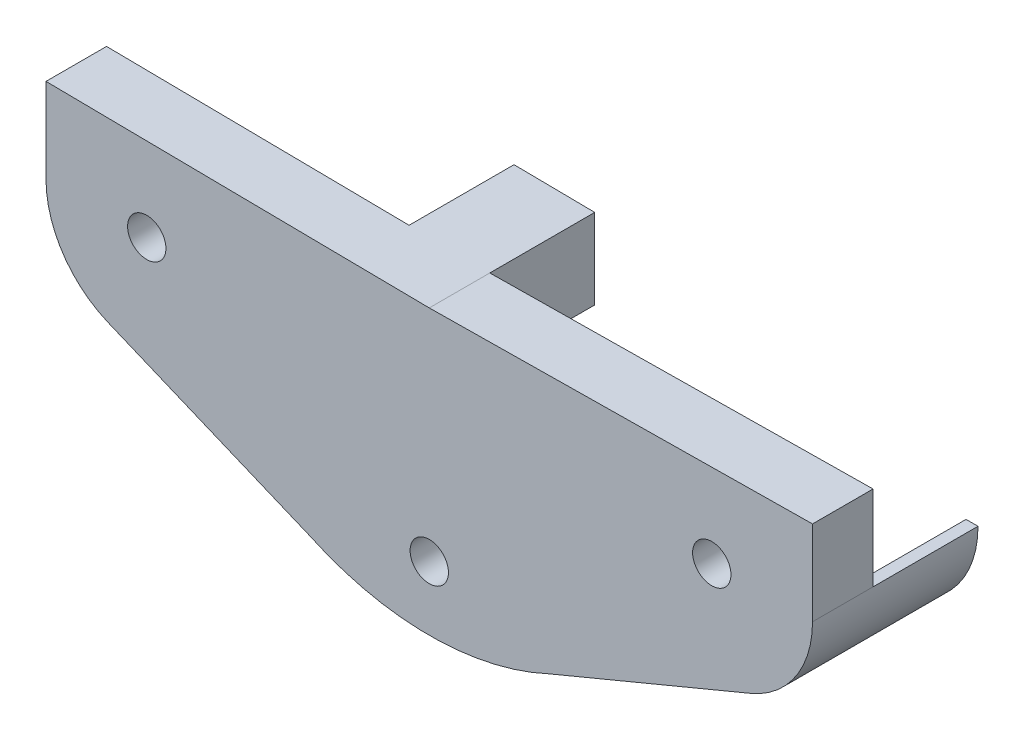
SolidWorks part; units mm, degrees
ref_plane "前视基准面" through (0, 0, 0) normal (0, 0, 1) x (1, 0, 0)
ref_plane "上视基准面" through (0, 0, 0) normal (0, 1, 0) x (1, 0, 0)
ref_plane "右视基准面" through (0, 0, 0) normal (1, 0, 0) x (0, 0, -1)
sketch "草图1" plane through (0, 0, 0) normal (0, 0, 1) x (1, 0, 0)
  line L0 (0, 14.4266) -> (0, -15.1664) construction
  line L1 (5.9425, -8.6841) -> (15.918, -4.5332)
  line L2 (-18.9924, 0.0761) -> (-18.9924, 4.276)
  line L3 (-18.9924, 4.276) -> (0, 4.0495)
  line L4 (18.9924, 4.276) -> (0, 4.0495)
  line L5 (18.9924, 0.0761) -> (18.9924, 4.276)
  line L6 (-5.9425, -8.6841) -> (-15.918, -4.5332)
  circle A0 centre (-14, 0.0761) radius 0.95
  arc A2 (15.918, -4.5332) -> (18.9924, 0.0761) centre (14, 0.0761) ccw
  circle A3 centre (14, 0.0761) radius 0.95
  arc A4 (-15.918, -4.5332) -> (-18.9924, 0.0761) centre (-14, 0.0761) cw
  arc A5 (-5.9425, -8.6841) -> (5.9425, -8.6841) centre (0, 4.0495) ccw
  circle A7 centre (0, -6.8345) radius 0.95
  point P20 (0, 4.0495)
extrude "凸台-拉伸1" add sketch "草图1" along normal blind 3
sketch "草图2" plane through (0, 0, 0) normal (0, 0, -1) x (-1, 0, 0)
  line L0 (-15.918, -4.5332) -> (-15.6904, -3.9862)
  line L1 (0, 4.0495) -> (3.9997, 4.0972)
  line L3 (-18.4, 0.0761) -> (-19, 0.0761)
  line L4 (0, 4.0495) -> (0, 0.0761)
  line L5 (0, 4.0495) -> (18.9924, 4.276) construction
  line L6 (3.9997, 4.0972) -> (3.9997, 0)
  line L8 (3.9997, 0) -> (0, 0.0761)
  arc A0 (-18.4, 0.0761) -> (-15.6904, -3.9862) centre (-14, 0.0761) ccw
  arc A3 (-18.9924, 0.0761) -> (-15.918, -4.5332) centre (-14, 0.0761) ccw construction
  arc A4 (-18.9924, 0.0761) -> (-15.918, -4.5332) centre (-14, 0.0761) ccw
  arc M28 (-18.9924, 0.0761) -> (-15.918, -4.5332) centre (-14, 0.0761) ccw
  line M34 (18.9924, 4.276) -> (0, 4.0495)
extrude "凸台-拉伸2" add sketch "草图2" along normal blind 5.2 contours A0 L3 L0 M28 | L8 L6 L4 M34
